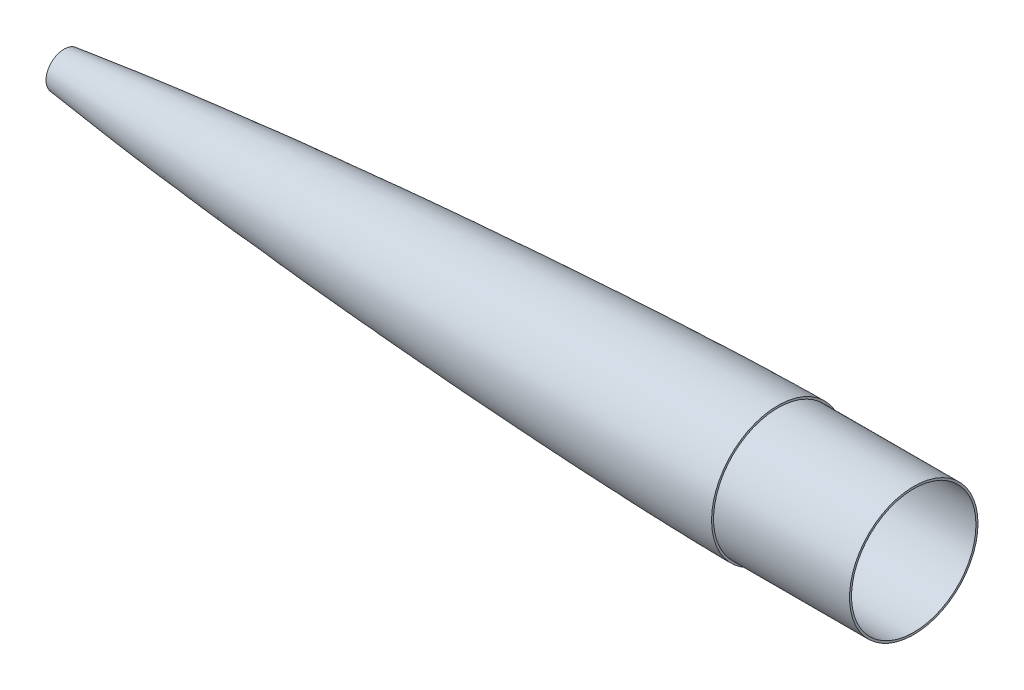
SolidWorks part; units mm, degrees
material "A-Glass Fiber"
ref_plane "Front Plane" through (0, 0, 0) normal (0, 0, 1) x (1, 0, 0)
ref_plane "Top Plane" through (0, 0, 0) normal (0, 1, 0) x (1, 0, 0)
ref_plane "Right Plane" through (0, 0, 0) normal (1, 0, 0) x (0, 0, -1)
sketch "Sketch1" plane through (0, 0, 0) normal (0, 0, 1) x (1, 0, 0)
  line L0 (609.7035, 49.5425) -> (0, 49.5425) construction
  line L1 (0, 0) -> (609.7035, 0) construction
  line L2 (609.7035, 0) -> (609.7035, 49.5425) construction
  line L4 (0, 0) -> (4.2432, 0)
  line L5 (609.7035, 49.5425) -> (609.7035, 48.0185)
  line L6 (76.2, 49.5425) -> (76.2, 0)
  line L7 (489.0535, 44.5691) -> (489.0535, 0) construction
  spline S0 degree 4 poles (0, 0) (0.0026, 0.0056) (0.0087, 0.0163) (0.0248, 0.0349) (0.0614, 0.0678) (0.1157, 0.1081) (0.188, 0.1546) (0.2908, 0.214) (0.4142, 0.2786) (0.5588, 0.3483) (0.7247, 0.4227) (0.9641, 0.524) (1.3347, 0.6697) (1.9693, 0.8979) (3.107, 1.2651) (5.1421, 1.8472) (8.9246, 2.7936) (16.0543, 4.3335) (28.7745, 6.6819) (49.7554, 9.994) (78.1202, 13.8444) (112.1347, 17.9128) (149.32, 21.9008) (186.5406, 25.5414) (223.7883, 28.8926) (261.0579, 31.9909) (298.3459, 34.8583) (335.6499, 37.5082) (372.9683, 39.947) (410.2999, 42.1753) (447.6438, 44.1872) (484.9994, 45.9696) (517.6955, 47.3072) (545.7276, 48.2682) (568.3263, 48.8964) (583.5347, 49.2341) (596.0246, 49.4397) (603.8409, 49.5199) (607.7493, 49.5425) (609.7035, 49.5425) knots 0 0 0 0 0 0.00004 0.00008 0.00016 0.000321 0.000481 0.000642 0.000936 0.00123 0.001529 0.001829 0.002633 0.003829 0.005933 0.009636 0.016455 0.029289 0.053563 0.094103 0.155164 0.216224 0.277285 0.338345 0.399406 0.460466 0.521526 0.582587 0.643647 0.704708 0.765768 0.826829 0.887889 0.918419 0.948949 0.974475 0.987237 1 1 1 1 1 construction
  spline S1 degree 4 poles (0, 0) (0.0026, 0.0056) (0.0087, 0.0163) (0.0248, 0.0349) (0.0614, 0.0678) (0.1157, 0.1081) (0.188, 0.1546) (0.2908, 0.214) (0.4142, 0.2786) (0.5588, 0.3483) (0.7247, 0.4227) (0.9641, 0.524) (1.3347, 0.6697) (1.9693, 0.8979) (3.107, 1.2651) (5.1421, 1.8472) (8.9246, 2.7936) (16.0543, 4.3335) (28.7745, 6.6819) (49.7554, 9.994) (78.1202, 13.8444) (112.1347, 17.9128) (149.32, 21.9008) (186.5406, 25.5414) (223.7883, 28.8926) (261.0579, 31.9909) (298.3459, 34.8583) (335.6499, 37.5082) (372.9683, 39.947) (410.2999, 42.1753) (447.6438, 44.1872) (484.9994, 45.9696) (517.6955, 47.3072) (545.7276, 48.2682) (568.3263, 48.8964) (583.5347, 49.2341) (596.0246, 49.4397) (603.8409, 49.5199) (607.7493, 49.5425) (609.7035, 49.5425) knots 0 0 0 0 0 0.00004 0.00008 0.00016 0.000321 0.000481 0.000642 0.000936 0.00123 0.001529 0.001829 0.002633 0.003829 0.005933 0.009636 0.016455 0.029289 0.053563 0.094103 0.155164 0.216224 0.277285 0.338345 0.399406 0.460466 0.521526 0.582587 0.643647 0.704708 0.765768 0.826829 0.887889 0.918419 0.948949 0.974475 0.987237 1 1 1 1 1
  spline S2 degree 1 poles (1.0385, -1.1154) (609.7035, 48.0185) knots 0 0 1 1 construction
  spline S3 degree 3 poles (1.0385, -1.1154) (1.0989, -1.083) (1.2128, -1.0279) (1.5232, -0.8922) (2.1055, -0.6677) (2.9562, -0.3824) (3.8274, -0.1188) (4.5739, 0.0949) (5.7537, 0.4193) (7.5186, 0.8678) (10.5921, 1.5877) (14.4643, 2.4134) (19.1367, 3.3301) (23.8239, 4.1916) (30.089, 5.283) (37.9399, 6.5629) (47.381, 7.9992) (59.9884, 9.8123) (75.7734, 11.9237) (94.7431, 14.2755) (113.7321, 16.4844) (132.7363, 18.5735) (158.0914, 21.2218) (189.8103, 24.3062) (227.9026, 27.7085) (266.0186, 30.8488) (304.1542, 33.7496) (342.3067, 36.4242) (393.1966, 39.6957) (438.932, 42.2396) (478.3176, 44.1042) (503.7895, 45.214) (534.4517, 46.3896) (565.1178, 47.3188) (590.6059, 47.8413) (603.3361, 48.0185) (609.7035, 48.0185) knots 0.000645 0.000645 0.000645 0.000645 0.001133 0.001621 0.002597 0.004549 0.006234 0.00721 0.008452 0.012356 0.01626 0.024067 0.031875 0.039682 0.04749 0.063105 0.078719 0.094334 0.125564 0.156794 0.188024 0.219254 0.250484 0.312943 0.375403 0.437863 0.500322 0.562782 0.625242 0.750161 0.787197 0.818427 0.875081 0.93754 0.96877 1 1 1 1
  dimension "D1" = 1.524
  dimension "D2" = 76.2
  dimension "D3" = 120.65
revolve "Revolve1" add sketch "Sketch1" angle 360 about L1
sketch "Sketch2" plane through (609.7035, 0, 0) normal (1, 0, 0) x (0, 0, -1)
  circle A0 centre (0, 0) radius 48.0185
  circle A2 centre (0, 0) radius 48.0185 construction
  circle A4 centre (0, 0) radius 46.4945
  dimension "D1" = 1.524
extrude "Boss-Extrude1" add sketch "Sketch2" along normal blind 101.6 and the other way blind 25.4
